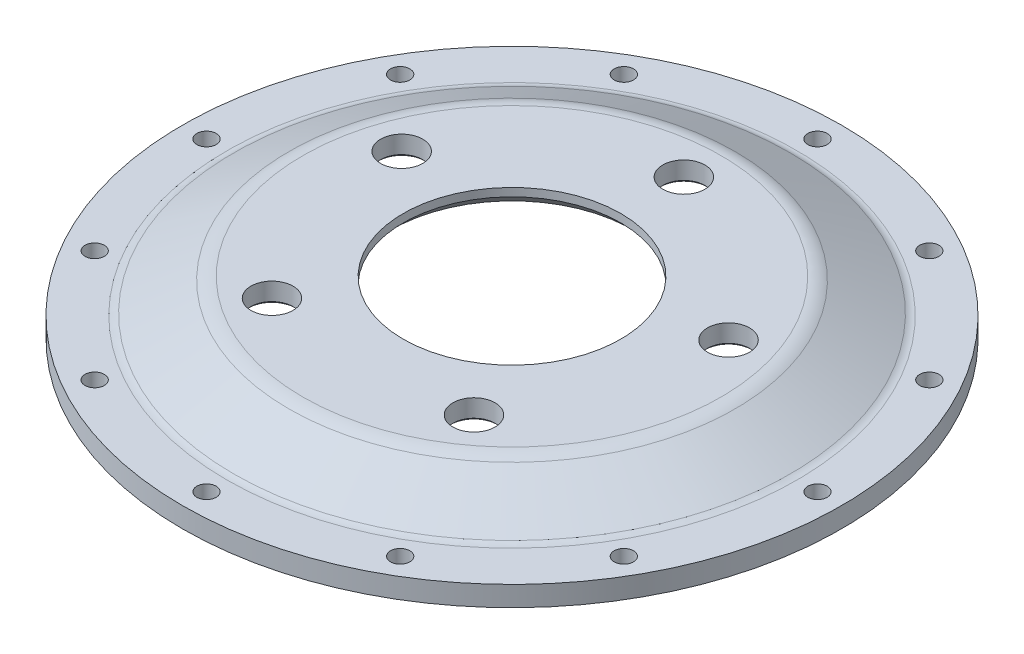
SolidWorks part; units mm, degrees
ref_plane "Front Plane" through (0, 0, 0) normal (0, 0, 1) x (1, 0, 0)
ref_plane "Top Plane" through (0, 0, 0) normal (0, 1, 0) x (1, 0, 0)
ref_plane "Right Plane" through (0, 0, 0) normal (1, 0, 0) x (0, 0, -1)
sketch "Sketch1" plane through (0, 0, 0) normal (0, 1, 0) x (1, 0, 0)
  line L0 (0, 118.5349) -> (0, -119.9893) construction
  line L1 (-24.3339, 109.6) -> (25.0755, 109.6) construction
  circle A0 centre (0, 0) radius 109.6
  circle A1 centre (0, 101.6) radius 3.2125
  circle A2 centre (0, 0) radius 93.6
  circle A3 centre (50.8, 87.9882) radius 3.2125
  circle A4 centre (87.9882, 50.8) radius 3.2125
  circle A5 centre (101.6, 0) radius 3.2125
  circle A6 centre (87.9882, -50.8) radius 3.2125
  circle A7 centre (50.8, -87.9882) radius 3.2125
  circle A8 centre (0, -101.6) radius 3.2125
  circle A9 centre (-50.8, -87.9882) radius 3.2125
  circle A10 centre (-87.9882, -50.8) radius 3.2125
  circle A11 centre (-101.6, 0) radius 3.2125
  circle A12 centre (-87.9882, 50.8) radius 3.2125
  circle A13 centre (-50.8, 87.9882) radius 3.2125
  point P28 (0, 0)
  point P33 (0, 0)
  point P37 (0, 0)
  dimension "D1" = 8
  dimension "D2" = 6.425
  dimension "D6" = 12
  dimension "D5" = 16
  dimension "D4" = 101.6
extrude "Boss-Extrude1" add sketch "Sketch1" along normal blind 6.7
ref_plane "Wheel Mounting Face" through (0, 17.95, 0) normal (0, 1, 0) x (1, 0, 0)
sketch "Sketch2" plane through (0, 17.95, 0) normal (0, 1, 0) x (1, 0, 0)
  circle A0 centre (0, 0) radius 72
  circle A1 centre (0, 0) radius 36.2
  circle A2 centre (0, 57.15) radius 7
  circle A3 centre (54.3529, 17.6603) radius 7
  circle A4 centre (33.5919, -46.2353) radius 7
  circle A5 centre (-33.5919, -46.2353) radius 7
  circle A6 centre (-54.3529, 17.6603) radius 7
  circle A7 centre (0, 0) radius 57.15 construction
  point P16 (0, 0)
  dimension "D1" = 144
  dimension "D2" = 72.4
  dimension "D3" = 14
  dimension "D6" = 114.3
  dimension "D4" = 57.15
  dimension "D5" = 5
extrude "Boss-Extrude3" add sketch "Sketch2" against normal blind 6.7 separate body
sketch "Sketch3" [suppressed] plane through (0, 0, 0) normal (0, 0, 1) x (1, 0, 0)
  line L0 (-73.355, 19.5) -> (-88.8, 6.7)
  line L1 (-88.8, 6.7) -> (-88.8, 0)
  line L3 (-73.355, 12.8) -> (-73.355, 19.5)
  line L4 (-73.355, 19.5) -> (-73.2286, 19.6264)
  line L5 (-88.8, 0) -> (-73.355, 12.8)
  line L6 (-73.355, 19.5) -> (-73.355, 12.8) construction
surface "Surface-Fill7" [suppressed]
surface "Surface-Fill8" [suppressed]
sketch "Sketch4" plane through (0, 0, 0) normal (0, 0, 1) x (1, 0, 0)
  line L0 (72, 17.95) -> (93.6, 6.7)
  line L1 (72, 11.25) -> (93.6, 0)
  line L4 (93.6, 6.7) -> (93.6, 0)
  line L5 (109.8492, 0) -> (75.9796, 0) construction
  line L7 (72, 11.25) -> (72, 17.95)
  dimension "D1" = 6.7
sweep "Sweep3" add profiles "Sketch4" path edge at (0, 11.25, 72)
fillet "Fillet1" radius 10 1 edges at (0, 17.95, 72)
fillet "Fillet2" radius 5 1 edges at (0, 6.7, 93.6)
chamfer "Chamfer1" distance 4 angle 45 1 edges at (0, 11.25, 36.2)
chamfer "Chamfer2" distance 0.8 angle 45 5 edges at (0, 11.25, -50.15) (54.3529, 11.25, -10.6603) (33.5919, 11.25, 53.2353) (-33.5919, 11.25, 53.2353) (-54.3529, 11.25, -10.6603)
fillet "Fillet7" radius 2.5 1 edges at (0, 11.25, -72)
fillet "Fillet8" radius 2.5 1 edges at (0, 0, -93.6)
equation "\"D5@Sketch1\"=\"D1@Sketch1\"*2"
